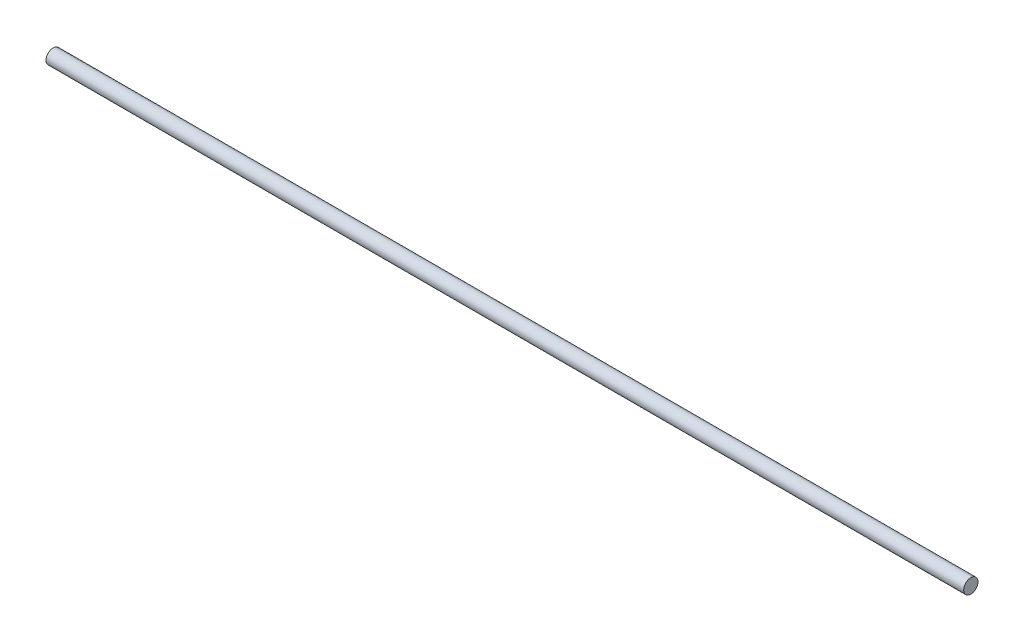
SolidWorks part; units mm, degrees
ref_plane "Front Plane" through (0, 0, 0) normal (0, 0, 1) x (1, 0, 0)
ref_plane "Top Plane" through (0, 0, 0) normal (0, 1, 0) x (1, 0, 0)
ref_plane "Right Plane" through (0, 0, 0) normal (1, 0, 0) x (0, 0, -1)
sketch "Sketch1" plane through (0, 0, 0) normal (1, 0, 0) x (0, 0, -1)
  circle A0 centre (0, 0) radius 3.175
  dimension "D1" = 6.35
extrude "Boss-Extrude1" add sketch "Sketch1" along normal blind 406.4 contours A0
